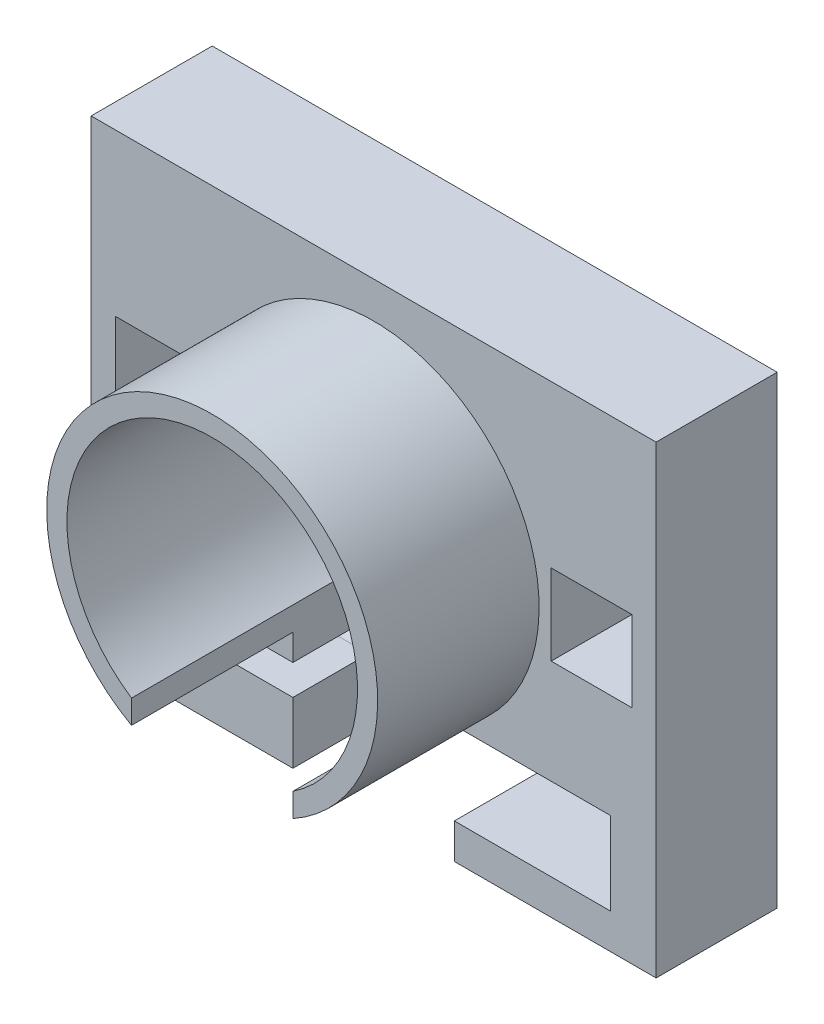
SolidWorks part; units mm, degrees
ref_plane "前基準面" through (0, 0, 0) normal (0, 0, 1) x (1, 0, 0)
ref_plane "上基準面" through (0, 0, 0) normal (0, 1, 0) x (1, 0, 0)
ref_plane "右基準面" through (0, 0, 0) normal (1, 0, 0) x (0, 0, -1)
sketch "草圖1" plane through (0, 0, 0) normal (0, 0, 1) x (1, 0, 0)
  line L1 (-61.4385, 56.9458) -> (78.5615, 56.9458)
  line L2 (-61.4385, 56.9458) -> (-61.4385, -58.0542)
  line L3 (-61.4385, -58.0542) -> (78.5615, -58.0542)
  line L4 (78.5615, 56.9458) -> (78.5615, -58.0542)
  line L5 (-55.4385, 16.9458) -> (-35.4385, 16.9458)
  line L6 (-55.4385, 16.9458) -> (-55.4385, -3.0542)
  line L7 (-55.4385, -3.0542) -> (-35.4385, -3.0542)
  line L8 (-35.4385, 16.9458) -> (-35.4385, -3.0542)
  line L9 (52.5615, 16.9458) -> (72.5615, 16.9458)
  line L10 (52.5615, 16.9458) -> (52.5615, -3.0542)
  line L11 (52.5615, -3.0542) -> (72.5615, -3.0542)
  line L12 (72.5615, 16.9458) -> (72.5615, -3.0542)
  circle A0 centre (8.5615, 6.9458) radius 36
  dimension "D9" = 72
  dimension "D12" = 50
  dimension "D13" = 70
  dimension "D1" = 140
  dimension "D2" = 115
  dimension "D3" = 6
  dimension "D4" = 6
  dimension "D5" = 20
  dimension "D6" = 20
  dimension "D7" = 20
  dimension "D8" = 20
  dimension "D10" = 40
  dimension "D11" = 40
extrude "填料-伸長1" add sketch "草圖1" along normal blind 30
sketch "草圖2" plane through (0, 0, 0) normal (0, 0, -1) x (-1, 0, 0)
  circle A0 centre (-8.5615, 6.9458) radius 40
  dimension "D1" = 80
extrude "除料-伸長1" cut sketch "草圖2" against normal blind 10
sketch "草圖10" plane through (0, 0, 30) normal (0, 0, 1) x (1, 0, 0)
  circle A0 centre (8.5615, 6.9458) radius 41
  circle A1 centre (8.5615, 6.9458) radius 36
  dimension "D1" = 82
extrude "填料-伸長3" add sketch "草圖10" along normal blind 40
sketch "草圖3" plane through (0, -58.0542, 0) normal (0, -1, 0) x (1, 0, 0)
  line L1 (-11.4385, 80) -> (28.5615, 80)
  line L2 (-11.4385, 80) -> (-11.4385, 0)
  line L3 (-11.4385, 0) -> (28.5615, 0)
  line L4 (28.5615, 80) -> (28.5615, 0)
  line L5 (-61.4385, 0) -> (78.5615, 0) construction
  line L6 (78.5615, 30) -> (78.5615, 0) construction
  dimension "D1" = 40
  dimension "D2" = 50
  dimension "D3" = 80
extrude "除料-伸長2" cut sketch "草圖3" against normal up to next
sketch "草圖4" plane through (-11.4385, 0, 0) normal (1, 0, 0) x (0, 0, -1)
  line L0 (-30, -28.8452) -> (-30, -58.0542) construction
  line L2 (-70, -28.8452) -> (-30, -28.8452) construction
  line L3 (-11.25, -42.8452) -> (-30, -42.8452)
  line L4 (-11.25, -42.8452) -> (-11.25, -35.3452)
  line L5 (-11.25, -35.3452) -> (-30, -35.3452)
  line L6 (-30, -42.8452) -> (-30, -35.3452)
  line L7 (0, -27.6952) -> (0, -58.0542) construction
  circle A0 centre (-11.25, -39.0952) radius 3.75
  line M1 (-30, -28.8452) -> (-30, -58.0542)
  dimension "D1" = 11.25
  dimension "D2" = 7.5
  dimension "D3" = 10.25
  dimension "D4" = 6.5
  dimension "D5" = 7.5
extrude "除料-伸長3" cut sketch "草圖4" against normal blind 15 contours A0 L5 L3 M1
sketch "草圖6" plane through (0, 0, 30) normal (0, 0, 1) x (1, 0, 0)
  line L1 (28.5615, -28.8452) -> (38.2115, -28.8452)
  line L2 (28.5615, -28.8452) -> (28.5615, -49.3452)
  line L3 (28.5615, -49.3452) -> (38.2115, -49.3452)
  line L4 (38.2115, -28.8452) -> (38.2115, -49.3452)
  dimension "D2" = 20.5
  dimension "D3" = 9.65
extrude "除料-伸長4" cut sketch "草圖6" against normal through all
sketch "草圖7" plane through (0, 0, 30) normal (0, 0, 1) x (1, 0, 0)
  line L1 (38.2115, -28.8452) -> (67.2115, -28.8452)
  line L2 (38.2115, -28.8452) -> (38.2115, -49.3452)
  line L3 (38.2115, -49.3452) -> (67.2115, -49.3452)
  line L4 (67.2115, -28.8452) -> (67.2115, -49.3452)
  dimension "D1" = 29
  dimension "D2" = 20.5
extrude "除料-伸長5" cut sketch "草圖7" against normal blind 21
sketch "草圖11" plane through (0, 0, 9) normal (0, 0, 1) x (1, 0, 0)
  line L0 (67.2115, -49.3452) -> (67.2115, -28.8452) construction
  line L1 (57.2115, -35.0952) -> (64.2115, -35.0952)
  line L2 (57.2115, -35.0952) -> (57.2115, -43.0952)
  line L3 (57.2115, -43.0952) -> (64.2115, -43.0952)
  line L4 (64.2115, -35.0952) -> (64.2115, -43.0952)
  line L5 (67.2115, -28.8452) -> (38.2115, -28.8452) construction
  dimension "D1" = 7
  dimension "D2" = 3
  dimension "D3" = 8
  dimension "D4" = 6.25
extrude "除料-伸長6" cut sketch "草圖11" against normal blind 10
